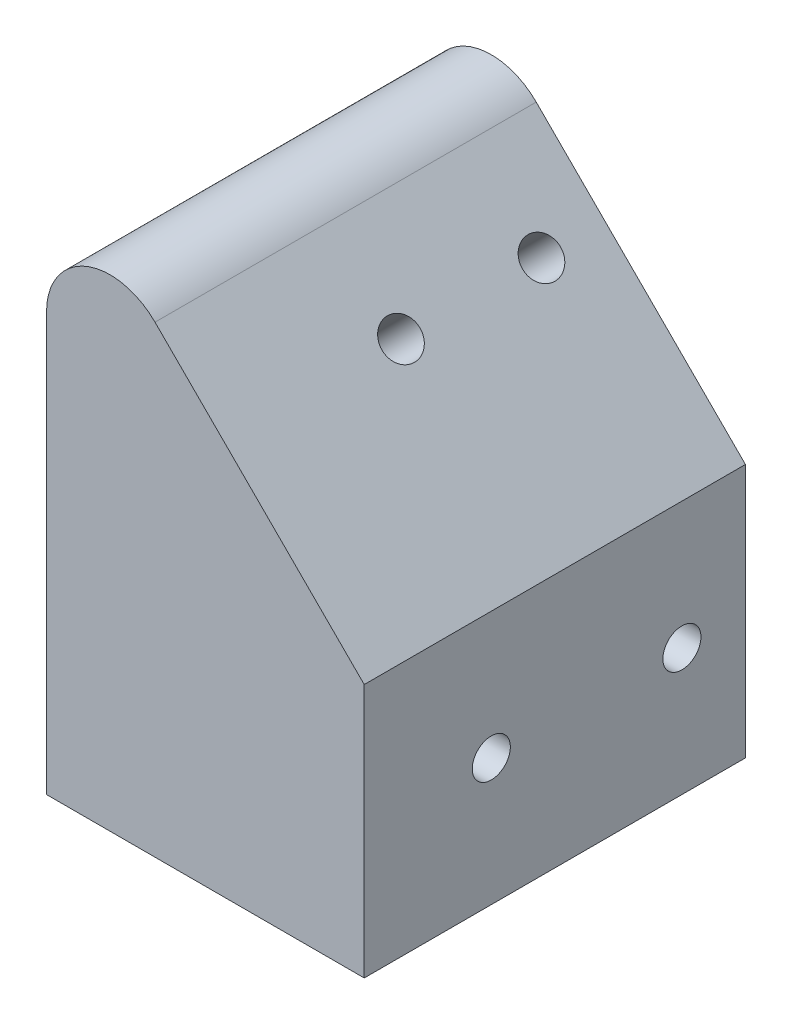
SolidWorks part; units mm, degrees
ref_plane "Alzado" through (0, 0, 0) normal (0, 0, 1) x (1, 0, 0)
ref_plane "Planta" through (0, 0, 0) normal (0, 1, 0) x (1, 0, 0)
ref_plane "Vista lateral" through (0, 0, 0) normal (1, 0, 0) x (0, 0, -1)
sketch "Croquis2" plane through (0, 0, 0) normal (1, 0, 0) x (0, 0, -1)
  line L0 (0, 0) -> (-30, 0)
  line L1 (0, 0) -> (-35.5397, 0) construction
  line L3 (0, -20) -> (-30, -20)
  line L7 (0, -20) -> (0, 0)
  line L8 (-30, -20) -> (-30, 0)
  line L10 (-35.5397, 0) -> (-75.7248, -24.1111) construction
  line L11 (-30, -20) -> (-55.7248, -35.4349) construction
  line L12 (-55.7248, -35.4349) -> (-55.7248, -45.4349) construction
  line L13 (-75.7248, -24.1111) -> (-75.7248, -45.4349) construction
  dimension "D1" = 30
  dimension "D4" = 20
extrude "Saliente-Extruir2" add sketch "Croquis2" along normal blind 25
sketch "Croquis3" plane through (0, 0, 0) normal (0, 0, -1) x (-1, 0, 0)
  line L0 (0, 0) -> (0, 25)
  line L1 (0, 25) -> (-25, 0)
  line L2 (-25, 0) -> (0, 0)
  dimension "D1" = 45
extrude "Saliente-Extruir3" add sketch "Croquis3" against normal through all
fillet "Redondeo1" radius 5 1 edges at (0, 25, 15)
sketch "Croquis8" plane through (0, 0, 0) normal (-1, 0, 0) x (0, 0, 1)
  circle A0 centre (20, -10) radius 1.5
  circle A1 centre (5, -10) radius 1.5
extrude "Cortar-Extruir5" cut sketch "Croquis8" against normal through all
sketch "Croquis9" plane through (12.5, 12.5, 0) normal (0.7071, 0.7071, 0) x (0, 0, -1)
  circle A0 centre (-16.0566, -2.0501) radius 1.5
  circle A1 centre (-5.0007, -2.0501) radius 1.5
extrude "Cortar-Extruir6" cut sketch "Croquis9" against normal through all
move or copy body "Sólido-Mover/Copiar1" [suppressed] bodies to move or copy 113
